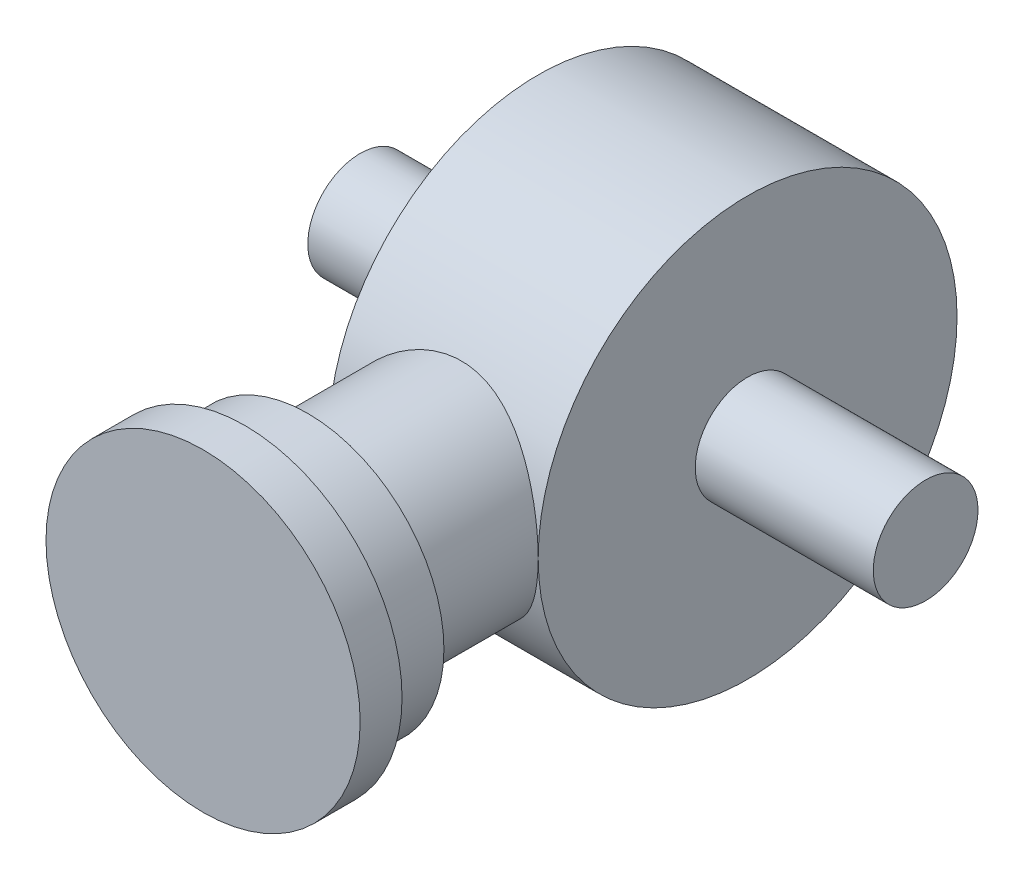
SolidWorks part; units mm, degrees
ref_plane "Alzado" through (0, 0, 0) normal (0, 0, 1) x (1, 0, 0)
ref_plane "Planta" through (0, 0, 0) normal (0, 1, 0) x (1, 0, 0)
ref_plane "Vista lateral" through (0, 0, 0) normal (1, 0, 0) x (0, 0, -1)
sketch "Croquis1" plane through (0, 0, 0) normal (1, 0, 0) x (0, 0, -1)
  circle A0 centre (0, 0) radius 25.4
  dimension "D1" = 50.8
extrude "Saliente-Extruir1" add sketch "Croquis1" along normal mid plane 25.4
ref_plane "Plano1" through (0, 0, 40.64) normal (0, 0, 1) x (1, 0, 0)
sketch "Croquis2" plane through (0, 0, 40.64) normal (0, 0, 1) x (1, 0, 0)
  circle A0 centre (0, 0) radius 12.7
extrude "Saliente-Extruir2" add sketch "Croquis2" against normal up to surface (15.24 mm away)
sketch "Croquis3" plane through (0, 0, 40.64) normal (0, 0, 1) x (1, 0, 0)
  circle A0 centre (0, 0) radius 16.51
  dimension "D1" = 33.02
extrude "Saliente-Extruir3" add sketch "Croquis3" along normal blind 7.62
sketch "Croquis4" plane through (0, 0, 48.26) normal (0, 0, 1) x (1, 0, 0)
  circle A0 centre (0, 0) radius 19.05
  dimension "D1" = 38.1
extrude "Saliente-Extruir4" add sketch "Croquis4" along normal blind 5.08
sketch "Croquis6" plane through (0, 0, 0) normal (1, 0, 0) x (0, 0, -1)
  circle A0 centre (0, 0) radius 6.35
  dimension "D1" = 12.7
extrude "Saliente-Extruir5" add sketch "Croquis6" along normal mid plane 68.58
